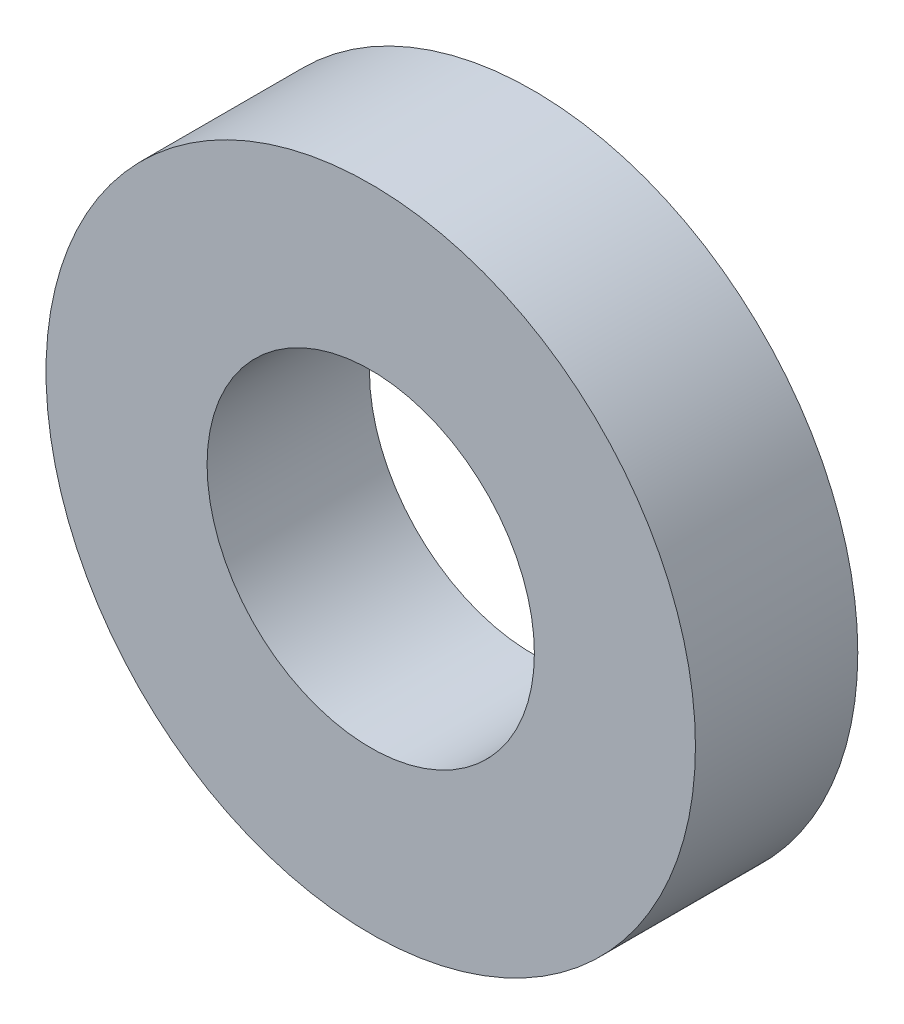
SolidWorks part; units mm, degrees
ref_plane "Front Plane" through (0, 0, 0) normal (0, 0, 1) x (1, 0, 0)
ref_plane "Top Plane" through (0, 0, 0) normal (0, 1, 0) x (1, 0, 0)
ref_plane "Right Plane" through (0, 0, 0) normal (1, 0, 0) x (0, 0, -1)
sketch "Sketch1" plane through (0, 0, 0) normal (0, 0, 1) x (1, 0, 0)
  circle A0 centre (0, 0) radius 6.35
  circle A1 centre (0, 0) radius 3.2004
  dimension "OD" = 12.7
  dimension "ID" = 6.4008
extrude "Extrude1" add sketch "Sketch1" along normal mid plane 3.175
sketch "Sketch2" plane through (0, 0, 0) normal (1, 0, 0) x (0, 0, -1)
  line L0 (-1.5875, -3.2004) -> (1.5875, -3.2004) construction
  line L3 (1.5875, 3.2004) -> (-1.5875, 3.2004) construction
  line L5 (-1.5875, -3.2004) -> (1.5875, -3.2004)
  line L6 (1.5875, 3.2004) -> (-1.5875, 3.2004)
sketch "Sketch4" plane through (0, 0, 1.5875) normal (0, 0, 1) x (1, 0, 0)
  line L0 (0, 0) -> (-2.263, 2.263)
  line L1 (0, -1.7463) -> (0, 1.7463) construction
  circle A0 centre (0, 0) radius 3.2004 construction
  dimension "D1" = 45
